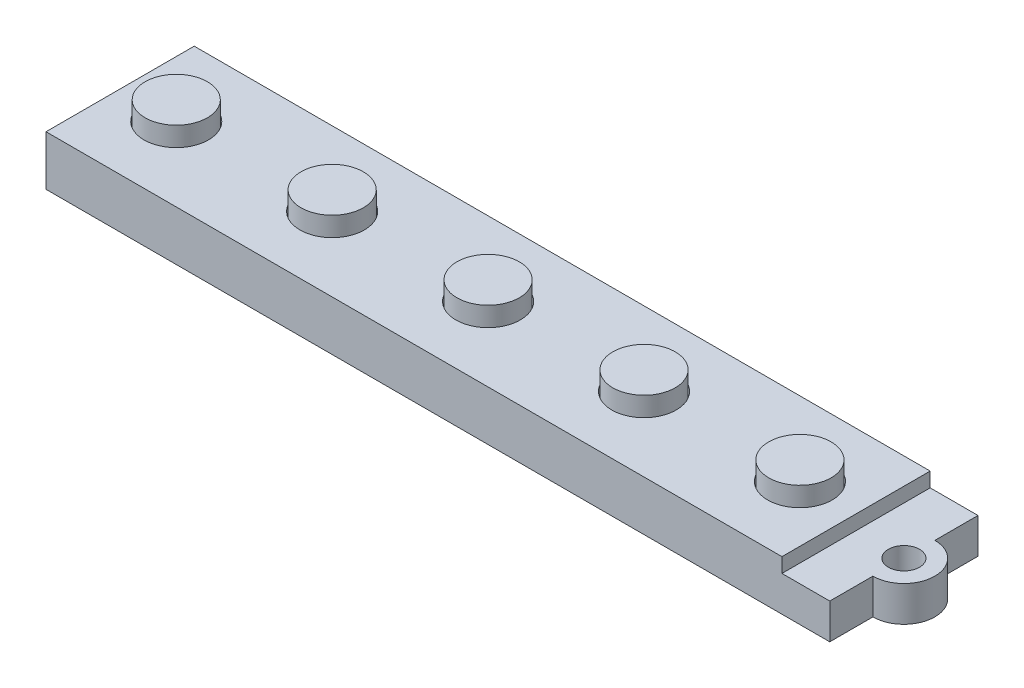
SolidWorks part; units mm, degrees
ref_plane "Front Plane" through (0, 0, 0) normal (0, 0, 1) x (1, 0, 0)
ref_plane "Top Plane" through (0, 0, 0) normal (0, 1, 0) x (1, 0, 0)
ref_plane "Right Plane" through (0, 0, 0) normal (1, 0, 0) x (0, 0, -1)
sketch "Sketch1" plane through (0, 0, 0) normal (0, 1, 0) x (1, 0, 0)
  line L1 (-116.1627, 34.9494) -> (-16.5947, 34.9494)
  line L2 (-116.1627, 34.9494) -> (-116.1627, 16.8392)
  line L3 (-116.1627, 16.8392) -> (-16.5947, 16.8392)
  line L4 (-16.5947, 34.9494) -> (-16.5947, 16.8392)
  dimension "D1" = 99.568
  dimension "D2" = 18.1102
extrude "Boss-Extrude1" add sketch "Sketch1" along normal blind 6.096
sketch "Sketch2" plane through (0, 6.096, 0) normal (0, 1, 0) x (1, 0, 0)
  line L0 (-16.5947, 34.9494) -> (-116.1627, 34.9494) construction
  line L1 (-26.2467, 34.9494) -> (-16.5947, 34.9494)
  line L2 (-26.2467, 34.9494) -> (-26.2467, 16.8392)
  line L3 (-26.2467, 16.8392) -> (-16.5947, 16.8392)
  line L4 (-16.5947, 34.9494) -> (-16.5947, 16.8392)
  line L5 (-116.1627, 34.9494) -> (-116.1627, 16.8392) construction
  dimension "D1" = 89.916
extrude "Cut-Extrude1" cut sketch "Sketch2" against normal blind 1.778
sketch "Sketch3" plane through (0, 4.318, 0) normal (0, 1, 0) x (1, 0, 0)
  line L0 (-20.4047, 34.9494) -> (-20.4047, 16.8392) construction
  line L1 (-16.5947, 34.9494) -> (-26.2467, 34.9494) construction
  line L2 (-26.2467, 16.8392) -> (-16.5947, 16.8392) construction
  line L3 (-16.5947, 16.8392) -> (-16.5947, 34.9494) construction
  circle A0 centre (-20.4047, 25.8943) radius 1.905
  dimension "D2" = 3.81
  dimension "D1" = 3.81
extrude "Cut-Extrude2" cut sketch "Sketch3" against normal through all
sketch "Sketch4" plane through (0, 6.096, 0) normal (0, 1, 0) x (1, 0, 0)
  line L0 (-26.2467, 34.9494) -> (-26.2467, 16.8392) construction
  circle A0 centre (-33.1047, 25.8943) radius 3.937
  circle A1 centre (-52.1547, 25.8943) radius 3.937
  circle A2 centre (-71.2047, 25.8943) radius 3.937
  circle A3 centre (-90.2547, 25.8943) radius 3.937
  circle A4 centre (-109.3047, 25.8943) radius 3.937
  dimension "D1" = 6.858
  dimension "D2" = 7.874
  dimension "D3" = 5
extrude "Cut-Extrude3" cut sketch "Sketch4" against normal blind 1.27
sketch "Sketch5" plane through (0, 0, 0) normal (0, -1, 0) x (1, 0, 0)
  line L0 (-26.2467, -34.9494) -> (-26.2467, -16.8392) construction
  line L1 (-16.5947, -34.9494) -> (-116.1627, -34.9494) construction
  line L2 (-116.1627, -16.8392) -> (-16.5947, -16.8392) construction
  line L3 (-116.1627, -34.9494) -> (-116.1627, -16.8392) construction
  line L4 (-116.1627, -34.9494) -> (-26.2467, -16.8392) construction
  line L6 (-29.9297, -32.2443) -> (-112.4797, -32.2443)
  line L7 (-29.9297, -32.2443) -> (-29.9297, -19.5443)
  line L8 (-29.9297, -19.5443) -> (-112.4797, -19.5443)
  line L9 (-112.4797, -32.2443) -> (-112.4797, -19.5443)
  line L10 (-29.9297, -32.2443) -> (-112.4797, -19.5443) construction
  line L11 (-29.9297, -19.5443) -> (-112.4797, -32.2443) construction
  point P9 (-71.2047, -25.8943)
  dimension "D1" = 89.916
  dimension "D2" = 12.7
  dimension "D3" = 82.55
extrude "Boss-Extrude2" add sketch "Sketch5" along normal blind 1.27
sketch "Sketch7" plane through (0, 4.318, 0) normal (0, 1, 0) x (1, 0, 0)
  line L0 (-20.4047, 34.9494) -> (-20.4047, 29.68) construction
  line L1 (-16.5947, 34.9494) -> (-26.2467, 34.9494) construction
  line L2 (-26.2467, 16.8392) -> (-16.5947, 16.8392) construction
  line L3 (-16.5947, 16.8392) -> (-16.5947, 34.9494) construction
  line L4 (-20.4047, 22.1085) -> (-20.4047, 16.8392) construction
  line L5 (-16.5947, 34.9494) -> (-20.4047, 34.9494)
  line L6 (-16.5947, 34.9494) -> (-16.5947, 16.8392)
  line L7 (-16.5947, 16.8392) -> (-20.4047, 16.8392)
  line L8 (-20.4047, 34.9494) -> (-20.4047, 29.68)
  line L9 (-20.4047, 22.1085) -> (-20.4047, 16.8392)
  arc A0 (-20.4047, 22.1085) -> (-20.4047, 29.68) centre (-20.4047, 25.8943) ccw
  dimension "D1" = 3.81
extrude "Cut-Extrude4" cut sketch "Sketch7" against normal through all
sketch "Sketch8" plane through (0, 4.826, 0) normal (0, 1, 0) x (1, 0, 0)
  circle A0 centre (-33.1047, 25.8943) radius 3.81
  circle A1 centre (-52.1547, 25.8943) radius 3.81
  circle A2 centre (-71.2047, 25.8943) radius 3.81
  circle A3 centre (-90.2547, 25.8943) radius 3.81
  circle A4 centre (-109.3047, 25.8943) radius 3.81
  dimension "D1" = 7.62
extrude "Boss-Extrude3" add sketch "Sketch8" along normal blind 3.556
